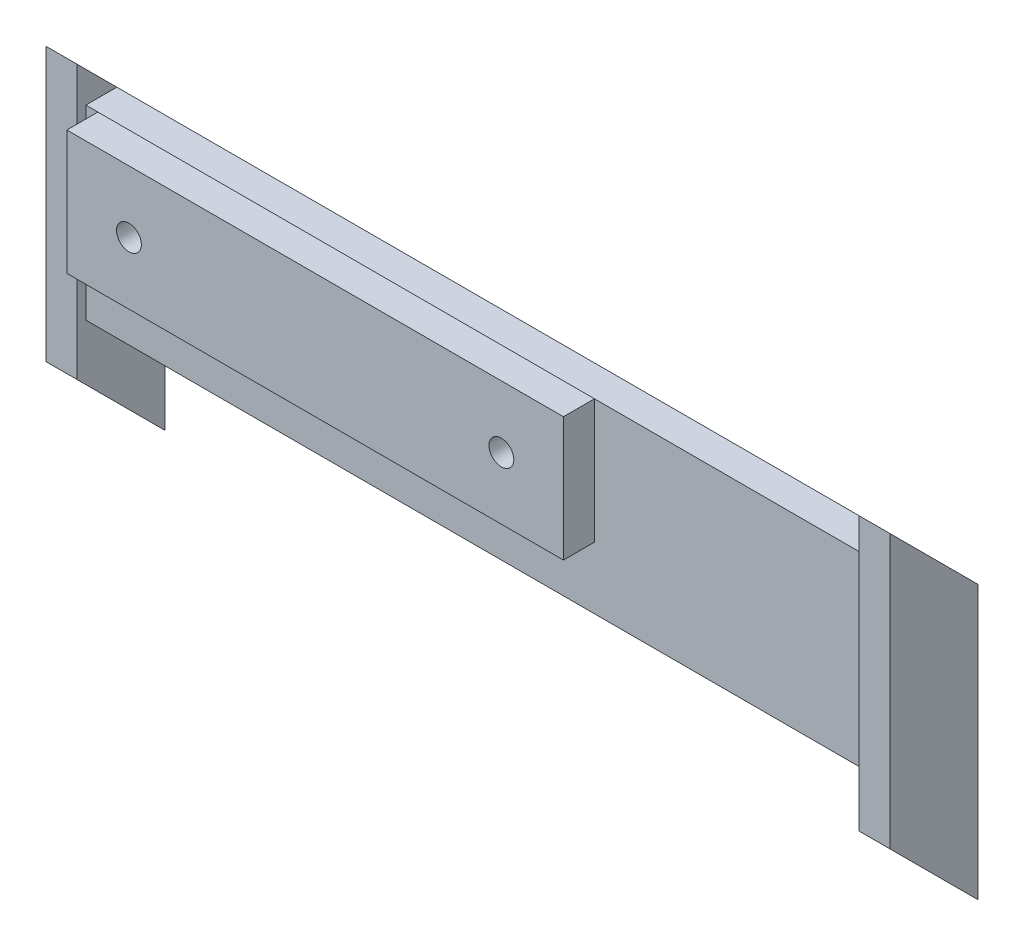
SolidWorks part; units mm, degrees
ref_plane "Front Plane" through (0, 0, 0) normal (0, 0, 1) x (1, 0, 0)
ref_plane "Top Plane" through (0, 0, 0) normal (0, 1, 0) x (1, 0, 0)
ref_plane "Right Plane" through (0, 0, 0) normal (1, 0, 0) x (0, 0, -1)
sketch "Sketch1" plane through (0, 0, 0) normal (0, 0, 1) x (1, 0, 0)
  line L0 (-39.8406, 15.4582) -> (40.1594, 15.4582)
  line L1 (40.1594, 15.4582) -> (40.1594, -4.5418)
  line L2 (40.1594, -4.5418) -> (-39.8406, -4.5418)
  line L3 (-39.8406, 15.4582) -> (-39.8406, -4.5418)
  circle A0 centre (-29.8406, 5.4582) radius 2
  circle A1 centre (30.1594, 5.4582) radius 2
  dimension "D3" = 4
  dimension "D4" = 4
  dimension "D1" = 80
  dimension "D2" = 20
  dimension "D5" = 60
  dimension "D6" = 10
  dimension "D7" = 10
  dimension "D8" = 10
extrude "Boss-Extrude1" add sketch "Sketch1" along normal blind 5
ref_plane "Plane1" through (12, 0, 0) normal (1, 0, 0) x (0, 0, -1)
ref_plane "Plane2" through (-12, 0, 0) normal (1, 0, 0) x (0, 0, -1)
sketch "Sketch2" plane through (12, 0, 0) normal (1, 0, 0) x (0, 0, -1)
  line L4 (0, 15.4582) -> (21.2132, -5.755)
  line L5 (0, -4.5418) -> (21.2132, -25.755)
  line L6 (-5, -4.5418) -> (0, -4.5418) construction
  line L7 (0, -4.5418) -> (0, 15.4582) construction
  line L9 (0, 15.4582) -> (0, -4.5418)
  line L10 (21.2132, -5.755) -> (21.2132, -25.755)
  dimension "D3" = 30
extrude "Boss-Extrude2" add sketch "Sketch2" along normal blind 5
sketch "Sketch3" plane through (-12, 0, 0) normal (1, 0, 0) x (0, 0, -1)
  line L5 (0, 15.4582) -> (21.2132, -5.755)
  line L6 (21.2132, -5.755) -> (0, 15.4582) construction
  line L7 (21.2132, -5.755) -> (21.2132, -25.755)
  line L8 (21.2132, -25.755) -> (0, -4.5418)
  line L9 (0, 15.4582) -> (0, -4.5418)
  dimension "D1" = 30
extrude "Boss-Extrude3" add sketch "Sketch3" against normal blind 5
sketch "Sketch4" plane through (0, 0, -21.2132) normal (0, 0, -1) x (-1, 0, 0)
  line L1 (-17, -5.755) -> (65, -5.755)
  line L2 (-17, -5.755) -> (-65, -5.755)
  line L4 (-65, -5.755) -> (-65, -35.755)
  line L6 (65, -4.5418) -> (65, -25.5615)
  line L7 (65, -5.755) -> (65, -35.755)
  line L10 (-65, -5.755) -> (-65, -25.1274)
  line L13 (-65, -25.1274) -> (-65, -32.8261)
  line L14 (65, -25.5615) -> (65, -32.8261)
  line L15 (-65, -35.755) -> (65, -35.755)
  point P11 (13.7188, -5.755)
  point P15 (38.1177, -5.755)
  point P17 (-36.2812, -5.755)
  point P18 (0, -25.5615)
  point P19 (38.1177, -25.705)
  point P20 (-36.2812, -25.1274)
  dimension "D1" = 50
  dimension "D2" = 24.3989
  dimension "D3" = 30
  dimension "D4" = 30
extrude "Boss-Extrude4" add sketch "Sketch4" along normal blind 5
ref_plane "Plane3" through (63, 0, 0) normal (1, 0, 0) x (0, 0, -1)
ref_plane "Plane4" through (-63, 0, 0) normal (-1, 0, 0) x (0, 0, 1)
sketch "Sketch6" plane through (63, 0, 0) normal (1, 0, 0) x (0, 0, -1)
  line L0 (26.2132, -5.755) -> (33.9411, -13.483)
  line L2 (33.9411, -50.554) -> (33.9411, -13.483)
  line L6 (33.9411, -55.554) -> (33.9411, -50.554)
  line L8 (26.2132, -5.755) -> (21.2132, -0.755)
  line L10 (21.2132, -44.755) -> (33.9411, -57.483)
  line L11 (33.9411, -55.554) -> (33.9411, -57.483)
  line L12 (21.2132, -0.755) -> (19.799, 0.6592)
  line L13 (21.2132, -44.755) -> (19.799, -43.3408)
  line L14 (19.799, 0.6592) -> (19.799, -43.3408)
  dimension "D1" = 18
  dimension "D2" = 44
  dimension "D3" = 2
  dimension "D4" = 2
extrude "Boss-Extrude9" add sketch "Sketch6" along normal blind 5
sketch "Sketch8" plane through (-63, 0, 0) normal (-1, 0, 0) x (0, 0, 1)
  line L0 (-19.799, 0.6592) -> (-33.9411, -13.483)
  line L1 (-33.9411, -13.483) -> (-33.9411, -57.483)
  line L2 (-33.9411, -57.483) -> (-19.799, -43.3408)
  line L3 (-19.799, -43.3408) -> (-19.799, 0.6592)
extrude "Boss-Extrude10" add sketch "Sketch8" along normal blind 5
